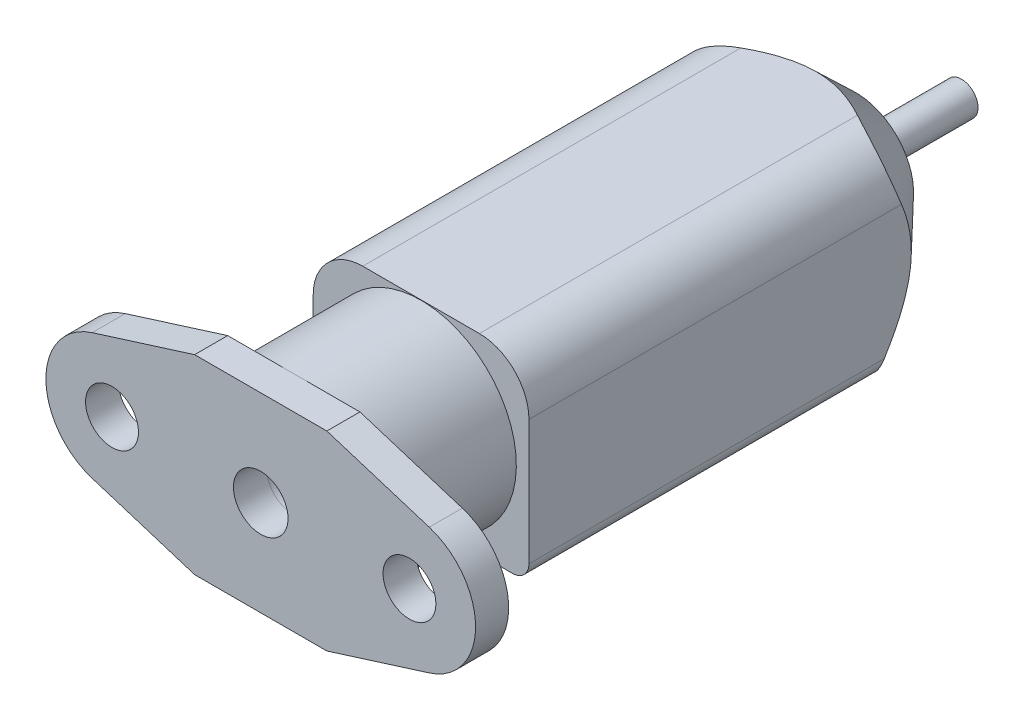
SolidWorks part; units mm, degrees
ref_plane "Alzado" through (0, 0, 0) normal (0, 0, 1) x (1, 0, 0)
ref_plane "Planta" through (0, 0, 0) normal (0, 1, 0) x (1, 0, 0)
ref_plane "Vista lateral" through (0, 0, 0) normal (1, 0, 0) x (0, 0, -1)
sketch "Croquis1" plane through (0, 0, 0) normal (0, 0, 1) x (1, 0, 0)
  line L0 (4, 5.763) -> (10.196, 3.8191)
  line L1 (-4, 5.763) -> (-10.1991, 3.8155)
  line L2 (-4, -5.765) -> (-10.1991, -3.8177)
  line L3 (4, -5.765) -> (10.1978, -3.8173)
  line L4 (4, -5.765) -> (-4, -5.765)
  line L5 (-4, 5.763) -> (4, 5.763)
  circle A0 centre (8.998, 0.0006) radius 1.5982
  circle A1 centre (-9.0001, -0.0011) radius 1.601
  circle A2 centre (0, 0) radius 1.6509
  arc A3 (10.1978, -3.8173) -> (10.196, 3.8191) centre (8.998, 0.0006) ccw
  arc A4 (-10.1991, 3.8155) -> (-10.1991, -3.8177) centre (-9.0001, -0.0011) ccw
extrude "Saliente-Extruir7" add sketch "Croquis1" against normal blind 2 separate body
sketch "Croquis2" plane through (0, 0, -2) normal (0, 0, -1) x (-1, 0, 0)
  circle A0 centre (0, 0) radius 5.765
  circle A1 centre (0, 0) radius 1.6512
extrude "Saliente-Extruir8" add sketch "Croquis2" along normal blind 7.7
sketch "Croquis3" plane through (0, 0, -9.7) normal (0, 0, -1) x (-1, 0, 0)
  line L1 (3.5269, 5.7838) -> (-3.5269, 5.7838)
  line L2 (6.5269, 2.7838) -> (6.5269, -4.7838)
  line L3 (5.5269, -5.7838) -> (-5.5269, -5.7838)
  line L4 (-6.5269, 2.7838) -> (-6.5269, -4.7838)
  line L5 (6.5269, 5.7838) -> (-6.5269, -5.7838) construction
  line L6 (6.5269, -5.7838) -> (-6.5269, 5.7838) construction
  arc A0 (-3.5269, 5.7838) -> (-6.5269, 2.7838) centre (-3.5269, 2.7838) ccw
  arc A1 (3.5269, 5.7838) -> (6.5269, 2.7838) centre (3.5269, 2.7838) cw
  arc A2 (-5.5269, -5.7838) -> (-6.5269, -4.7838) centre (-5.5269, -4.7838) cw
  arc A3 (6.5269, -4.7838) -> (5.5269, -5.7838) centre (5.5269, -4.7838) cw
  point P0 (0, 0)
  dimension "D1" = 3
  dimension "D2" = 1
extrude "Saliente-Extruir9" add sketch "Croquis3" along normal blind 26.3
ref_plane "Plano1" through (0, 5.765, 0) normal (0, 1, 0) x (1, 0, 0)
ref_axis "Eje1" through (0, 0, -39.9199) along (0, 0, 1)
sketch "Croquis5" plane through (0, 0, 0) normal (0, 1, 0) x (1, 0, 0)
  line L0 (0, 36) -> (-3.5, 36) construction
  line L1 (-3.5269, 36) -> (3.5269, 36) construction
  line L2 (-3.5, 36) -> (-8.4726, 30.8035)
  line L3 (-3.5, 36) -> (-8.4726, 36)
  line L4 (-8.4726, 30.8035) -> (-8.4726, 36)
revolve "Cortar-Revolución1" cut sketch "Croquis5" angle 360 about axis through (0, 0, -39.9199) along (0, 0, 1)
sketch "Croquis6" plane through (0, 0, -36) normal (0, 0, -1) x (-1, 0, 0)
  line L0 (0, 0.9994) -> (0, -0.9994) construction
  circle A0 centre (0, 0) radius 0.9994
extrude "Saliente-Extruir10" add sketch "Croquis6" along normal blind 6.4
sketch "Sketch1" plane through (0, 0, 0) normal (0, 0, 1) x (1, 0, 0)
  line L0 (0, -13.0021) -> (0, 13.0021) construction
  point P5 (0, 0)
